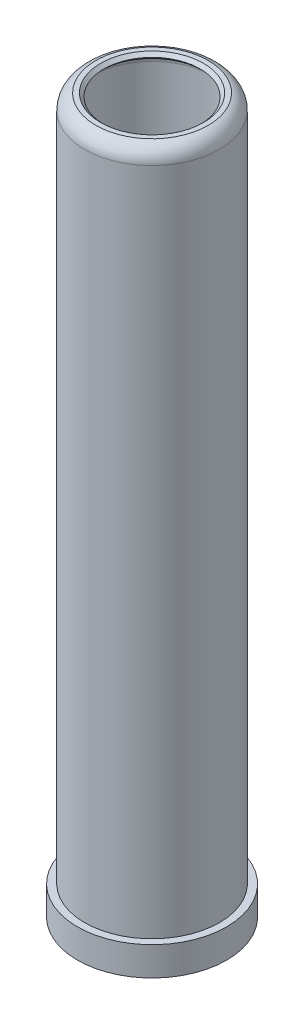
SolidWorks part; units mm, degrees
material "6061 Alloy"
ref_plane "Front Plane" through (0, 0, 0) normal (0, 0, 1) x (1, 0, 0)
ref_plane "Top Plane" through (0, 0, 0) normal (0, 1, 0) x (1, 0, 0)
ref_plane "Right Plane" through (0, 0, 0) normal (1, 0, 0) x (0, 0, -1)
sketch "Sketch1" plane through (0, 0, 0) normal (0, 0, 1) x (1, 0, 0)
  line L0 (0, -1085.2043) -> (0, 53175.0084) construction
  line L1 (12.5, 7) -> (12.5, 139.0669)
  line L2 (10.6731, 140.8938) -> (10, 141.5669)
  line L3 (10, 141.5669) -> (10.6731, 142.24)
  line L4 (10.6731, 142.24) -> (11.6731, 142.24)
  line L5 (14, 139.0669) -> (14, 0)
  line L6 (14, 0) -> (15.5, 0)
  line L7 (15.5, 0) -> (15.5, -6)
  line L8 (15.5, -6) -> (14.5, -6)
  line L9 (10, 2) -> (10, 7)
  line L10 (10, 7) -> (12.5, 7)
  line L11 (10, 2) -> (11, 2)
  line L12 (11, 2) -> (11, -1)
  line L13 (12.5, 0) -> (12.5, 7) construction
  arc A0 (12.5, 139.0669) -> (10.6731, 140.8938) centre (10.6731, 139.0669) ccw
  arc A1 (14, 139.0669) -> (11.6731, 142.24) centre (10.6731, 139.0669) ccw
  arc A2 (14.5, -6) -> (11, -1) centre (9.1786, -6) ccw
  dimension "D1" = 1.5
  dimension "D2" = 135
  dimension "D3" = 1
  dimension "D4" = 4
  dimension "D5" = 28
  dimension "D6" = 142.24
  dimension "D7" = 31
  dimension "D8" = 6
  dimension "D9" = 20
  dimension "D10" = 5
  dimension "D11" = 13
  dimension "D12" = 3
  dimension "D13" = 1
  dimension "D14" = 1
revolve "Revolve1" add sketch "Sketch1" angle 360 about L0
